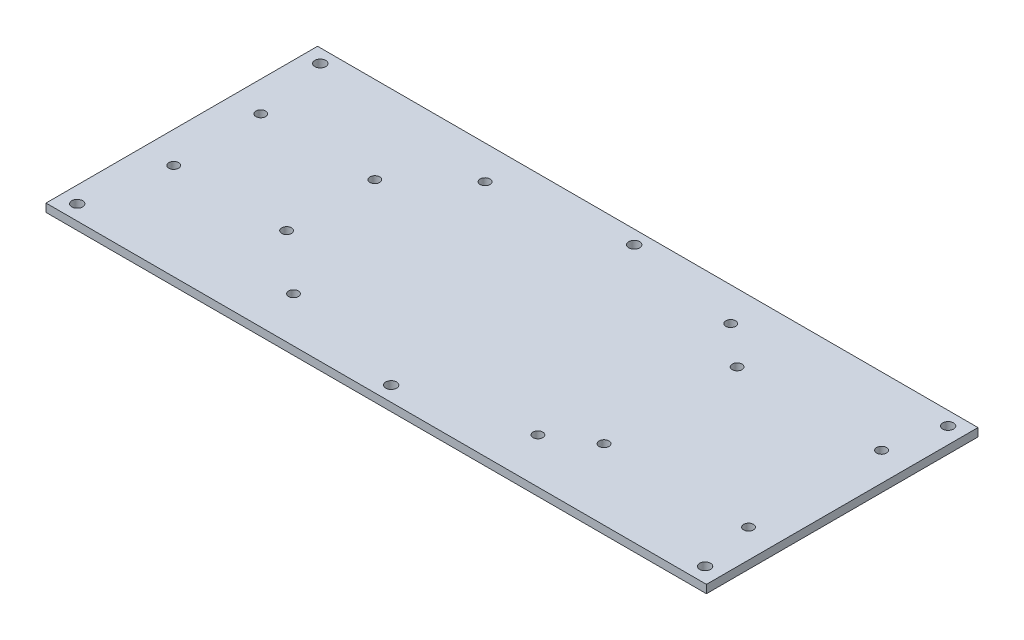
SolidWorks part; units mm, degrees
ref_plane "Front" through (0, 0, 0) normal (0, 0, 1) x (1, 0, 0)
ref_plane "Top" through (0, 0, 0) normal (0, 1, 0) x (1, 0, 0)
ref_plane "Right" through (0, 0, 0) normal (1, 0, 0) x (0, 0, -1)
sketch "底板" plane through (0, 0, 0) normal (0, 1, 0) x (1, 0, 0)
  line L13 (-1, 0) -> (242.2, 0)
  line L14 (-1, 0) -> (-1, -100)
  line L15 (-1, -100) -> (242.2, -100)
  line L16 (242.2, 0) -> (242.2, -100)
  circle A0 centre (73.0496, -12.3619) radius 1.8
  circle A1 centre (73.4956, -83.3605) radius 1.8
  circle A2 centre (163.4956, -12.3605) radius 1.8
  circle A3 centre (163.4956, -83.3605) radius 1.8
  circle A4 centre (10.0912, -32) radius 1.8
  circle A5 centre (10.5229, -64.4971) radius 1.8
  circle A6 centre (52.0912, -32) radius 1.8
  circle A7 centre (52.0912, -64.4971) radius 1.8
  circle A8 centre (120.6, -5) radius 2
  circle A9 centre (120.6, -94.5) radius 2
  circle A10 centre (5, -5) radius 2
  circle A11 centre (5, -94.5) radius 2
  circle A12 centre (236.2, -5) radius 2
  circle A13 centre (236.2, -94.5) radius 2
  circle A14 centre (231.6956, -25) radius 1.8
  circle A15 centre (231.6956, -74) radius 1.8
  circle A16 centre (178.4956, -74) radius 1.8
  circle A17 centre (178.4956, -25) radius 1.8
  point P8 (221.0628, -5)
  point P17 (221.0628, -94.5)
  point P18 (0, 0)
  point P21 (0, 0)
  point P26 (0, 0)
  point P27 (0, 0)
  point P28 (0, 0)
  point P31 (0, 0)
  point P34 (223.4829, -16.2769)
  point P37 (223.4829, -79.0533)
  point P46 (172.7872, -79.0533)
  point P47 (0, 0)
  point P50 (172.7872, -16.2769)
  point P51 (0, 0)
  point P52 (0, 0)
  point P53 (172.7872, -16.2769)
  point P54 (0, 0)
  point P55 (0, 0)
  point P56 (0, 0)
  point P57 (0, 0)
  point P58 (0, 0)
  point P59 (0, 0)
  point P60 (0, 0)
  point P61 (0, 0)
  dimension "D1" = 71
  dimension "D13" = 115.6
  dimension "D2" = 243.2
  dimension "D3" = 32.5
  dimension "D4" = 42
  dimension "D5" = 20.9584
  dimension "D6" = 90
  dimension "D7" = 71
  dimension "D8" = 89.5
  dimension "D9" = 100
  dimension "D10" = 32
  dimension "D11" = 115.6
  dimension "D12" = 6
  dimension "D14" = 49
  dimension "D15" = 53.2
  dimension "D16" = 15
  dimension "D17" = 25
extrude "凸台-拉伸3" add sketch "底板" along normal blind 3
